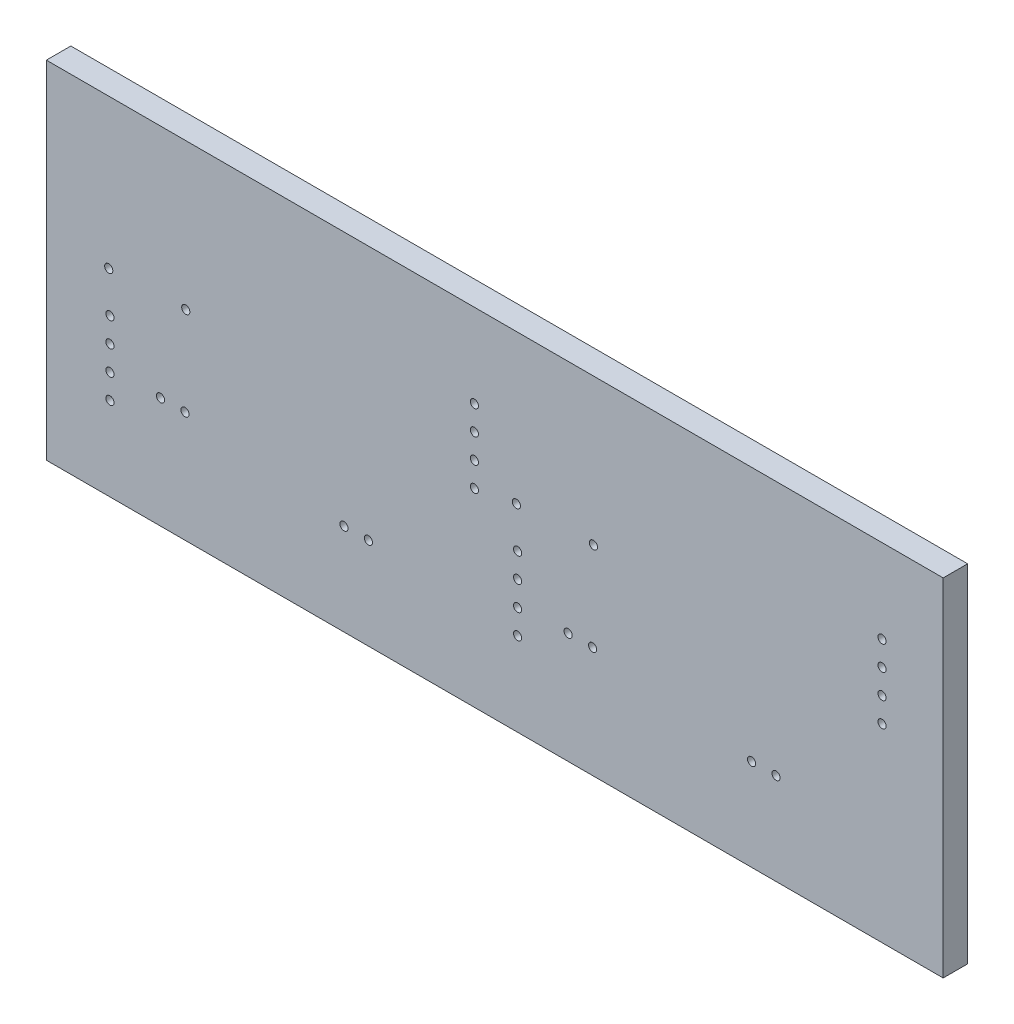
SolidWorks part; units mm, degrees
ref_plane "Plan de face" through (0, 0, 0) normal (0, 0, 1) x (1, 0, 0)
ref_plane "Plan de dessus" through (0, 0, 0) normal (0, 1, 0) x (1, 0, 0)
ref_plane "Plan de droite" through (0, 0, 0) normal (1, 0, 0) x (0, 0, -1)
sketch "Esquisse1" plane through (0, 0, 0) normal (0, 0, 1) x (1, 0, 0)
  line L0 (97.3951, 0) -> (-118.5049, 0) construction
  line L1 (-165, 119) -> (165, 119)
  line L2 (-165, 119) -> (-165, -119)
  line L3 (-165, -119) -> (165, -119)
  line L4 (165, 119) -> (165, -119)
  line L5 (0, 79.3588) -> (0, -79.3588) construction
  line L6 (-92.5, -55) -> (-77.5, -55)
  line L7 (-92.5, -55) -> (-92.5, -61)
  line L8 (-92.5, -61) -> (-77.5, -61)
  line L9 (-77.5, -55) -> (-77.5, -61)
  line L10 (-7.5, -55) -> (7.5, -55)
  line L11 (-7.5, -55) -> (-7.5, -61)
  line L12 (-7.5, -61) -> (7.5, -61)
  line L13 (7.5, -55) -> (7.5, -61)
  line L14 (77.5, -55) -> (92.5, -55)
  line L15 (77.5, -55) -> (77.5, -61)
  line L16 (77.5, -61) -> (92.5, -61)
  line L17 (92.5, -55) -> (92.5, -61)
  line L18 (-225.3679, 76) -> (203.1013, 76) construction
  line L19 (55, 99) -> (75, 99)
  line L20 (55, 99) -> (55, 93)
  line L21 (55, 93) -> (75, 93)
  line L22 (75, 99) -> (75, 93)
  line L23 (85, 99) -> (105, 99)
  line L24 (85, 99) -> (85, 93)
  line L25 (85, 93) -> (105, 93)
  line L26 (105, 99) -> (105, 93)
  circle A0 centre (-125, 76) radius 8
  circle A1 centre (125, 76) radius 8
  dimension "D23" = 16
  dimension "D24" = 16
  dimension "D1" = 238
  dimension "D2" = 330
  dimension "D3" = 165
  dimension "D4" = 119
  dimension "D5" = 15
  dimension "D6" = 6
  dimension "D7" = 6
  dimension "D8" = 15
  dimension "D9" = 6
  dimension "D10" = 15
  dimension "D11" = 70
  dimension "D12" = 70
  dimension "D13" = 58
  dimension "D14" = 72.5
  dimension "D15" = 6
  dimension "D16" = 20
  dimension "D17" = 20
  dimension "D18" = 6
  dimension "D19" = 10
  dimension "D20" = 60
  dimension "D21" = 20
  dimension "D22" = 20
  dimension "D25" = 40
  dimension "D26" = 40
  dimension "D27" = 195
extrude "Boss.-Extru.1" add sketch "Esquisse1" along normal blind 6
sketch "Esquisse2" plane through (0, 0, 6) normal (0, 0, 1) x (1, 0, 0)
  line L0 (243.146, 0) -> (-260.0003, 0) construction
  line L1 (0, 180.4713) -> (0, -129.6072) construction
  line L2 (175, 124) -> (-175, 124) construction
  line L3 (-125, 124) -> (-105, 124)
  line L4 (-125, 124) -> (-125, 130)
  line L5 (-125, 130) -> (-105, 130)
  line L6 (-105, 124) -> (-105, 130)
  line L7 (-175, 124) -> (-175, -124) construction
  line L8 (-55, 124) -> (-35, 124)
  line L9 (-55, 124) -> (-55, 130)
  line L10 (-55, 130) -> (-35, 130)
  line L11 (-35, 124) -> (-35, 130)
  line L12 (35, 124) -> (35, 130)
  line L13 (55, 130) -> (35, 130)
  line L14 (55, 124) -> (55, 130)
  line L15 (55, 124) -> (35, 124)
  line L16 (105, 124) -> (105, 130)
  line L17 (125, 130) -> (105, 130)
  line L18 (125, 124) -> (125, 130)
  line L19 (125, 124) -> (105, 124)
  line L20 (-125, 124) -> (-105, 124)
  line L21 (-125, 124) -> (-125, 130)
  line L22 (-125, 130) -> (-105, 130)
  line L23 (-105, 124) -> (-105, 130)
  line L24 (-55, 124) -> (-35, 124)
  line L25 (-55, 124) -> (-55, 130)
  line L26 (-55, 130) -> (-35, 130)
  line L27 (-35, 124) -> (-35, 130)
  line L28 (35, 124) -> (35, 130)
  line L29 (55, 130) -> (35, 130)
  line L30 (55, 124) -> (55, 130)
  line L31 (55, 124) -> (35, 124)
  line L32 (105, 124) -> (105, 130)
  line L33 (125, 130) -> (105, 130)
  line L34 (125, 124) -> (125, 130)
  line L35 (125, 124) -> (105, 124)
  line L36 (125, -124) -> (105, -124)
  line L37 (125, -124) -> (125, -130)
  line L38 (125, -130) -> (105, -130)
  line L39 (105, -124) -> (105, -130)
  line L40 (55, -124) -> (35, -124)
  line L41 (55, -124) -> (55, -130)
  line L42 (55, -130) -> (35, -130)
  line L43 (35, -124) -> (35, -130)
  line L44 (-35, -124) -> (-35, -130)
  line L45 (-55, -130) -> (-35, -130)
  line L46 (-55, -124) -> (-55, -130)
  line L47 (-55, -124) -> (-35, -124)
  line L48 (-105, -124) -> (-105, -130)
  line L49 (-125, -130) -> (-105, -130)
  line L50 (-125, -124) -> (-125, -130)
  line L51 (-125, -124) -> (-105, -124)
  line L52 (125, -124) -> (105, -124)
  line L53 (125, -124) -> (125, -130)
  line L54 (125, -130) -> (105, -130)
  line L55 (105, -124) -> (105, -130)
  line L56 (55, -124) -> (35, -124)
  line L57 (55, -124) -> (55, -130)
  line L58 (55, -130) -> (35, -130)
  line L59 (35, -124) -> (35, -130)
  line L60 (-35, -124) -> (-35, -130)
  line L61 (-55, -130) -> (-35, -130)
  line L62 (-55, -124) -> (-55, -130)
  line L63 (-55, -124) -> (-35, -124)
  line L64 (-105, -124) -> (-105, -130)
  line L65 (-125, -130) -> (-105, -130)
  line L66 (-125, -124) -> (-125, -130)
  line L67 (-125, -124) -> (-105, -124)
  line M9 (-175, -124) -> (175, -124)
  line M11 (175, 124) -> (-175, 124)
  dimension "D1" = 6
  dimension "D2" = 6
  dimension "D3" = 20
  dimension "D4" = 20
  dimension "D5" = 50
  dimension "D6" = 50
extrude "Boss.-Extru.2" add sketch "Esquisse2" against normal blind 6 contours L6 L5 L4 M11 | L11 L10 L9 M11 | L14 L13 L12 M11 | L18 L17 L16 M11 | L39 L38 L37 M9 | L43 L42 L41 M9 | L46 L45 L44 M9 | L50 L49 L48 M9
sketch "Esquisse3" plane through (0, 0, 6) normal (0, 0, 1) x (1, 0, 0)
  line L0 (-175, 124) -> (-175, -124) construction
  line L1 (-175, 74) -> (-169, 74)
  line L2 (-175, 74) -> (-175, 94)
  line L3 (-175, 94) -> (-169, 94)
  line L4 (-169, 74) -> (-169, 94)
  line L5 (234.1368, 0) -> (-337.9213, 0) construction
  line L6 (-175, 34) -> (-169, 34)
  line L7 (-175, 34) -> (-175, 14)
  line L8 (-175, 14) -> (-169, 14)
  line L9 (-169, 34) -> (-169, 14)
  line L10 (0, 279.7488) -> (0, -188.1201) construction
  line L11 (-125, 124) -> (-175, 124) construction
  line L12 (-169, -34) -> (-169, -14)
  line L13 (-175, -14) -> (-169, -14)
  line L14 (-175, -34) -> (-175, -14)
  line L15 (-175, -34) -> (-169, -34)
  line L16 (-169, -74) -> (-169, -94)
  line L17 (-175, -94) -> (-169, -94)
  line L18 (-175, -74) -> (-175, -94)
  line L19 (-175, -74) -> (-169, -74)
  line L20 (175, -74) -> (169, -74)
  line L21 (175, -74) -> (175, -94)
  line L22 (175, -94) -> (169, -94)
  line L23 (169, -74) -> (169, -94)
  line L24 (175, -34) -> (169, -34)
  line L25 (175, -34) -> (175, -14)
  line L26 (175, -14) -> (169, -14)
  line L27 (169, -34) -> (169, -14)
  line L28 (169, 34) -> (169, 14)
  line L29 (175, 14) -> (169, 14)
  line L30 (175, 34) -> (175, 14)
  line L31 (175, 34) -> (169, 34)
  line L32 (169, 74) -> (169, 94)
  line L33 (175, 94) -> (169, 94)
  line L34 (175, 74) -> (175, 94)
  line L35 (175, 74) -> (169, 74)
  line L36 (163, -124) -> (163, -114)
  line L37 (-175, -124) -> (-163, -124)
  line L38 (-175, -124) -> (-175, -114)
  line L39 (-175, -114) -> (-163, -114)
  line L40 (-163, -124) -> (-163, -114)
  line L41 (175, -114) -> (163, -114)
  line L42 (175, -124) -> (175, -114)
  line L43 (175, -124) -> (163, -124)
  dimension "D1" = 40
  dimension "D2" = 6
  dimension "D3" = 6
  dimension "D4" = 20
  dimension "D5" = 20
  dimension "D6" = 30
  dimension "D7" = 12
  dimension "D8" = 10
extrude "Enlèv. mat.-Extru.1" cut sketch "Esquisse3" against normal blind 6
sketch "Esquisse4" plane through (0, 0, 6) normal (0, 0, 1) x (1, 0, 0)
  line L0 (-172, 127) -> (-172, -131.0602) construction
  line L1 (0, 158.5579) -> (0, -182.4489) construction
  line L2 (-125, 124) -> (-175, 124) construction
  line L3 (-106.4439, -58) -> (117.3944, -58) construction
  line L4 (-169, 94) -> (-175, 94) construction
  line L5 (-175, 124) -> (-175, 94) construction
  line L6 (-175, 74) -> (-169, 74) construction
  line L7 (-169, 34) -> (-175, 34) construction
  line L8 (-175, 14) -> (-169, 14) construction
  line L9 (-169, -14) -> (-175, -14) construction
  line L10 (-102.5, -60) -> (-102.5, -66) construction
  line L11 (-87.5, -66) -> (-87.5, -60) construction
  line L12 (-175, -34) -> (-169, -34) construction
  line L13 (-169, -74) -> (-175, -74) construction
  line L14 (-175, -94) -> (-169, -94) construction
  line L15 (-17.5, -60) -> (-17.5, -66) construction
  line L16 (172, 127) -> (172, -131.0602) construction
  line L17 (136.5184, 101) -> (43.4816, 101) construction
  line L18 (-126.5544, 127) -> (2.7821, 127) construction
  line L19 (-55, 124) -> (-105, 124) construction
  line L20 (-55, 124) -> (-55, 130) construction
  line L21 (85, 98) -> (85, 104) construction
  line L23 (65, 98) -> (85, 98) construction
  circle A0 centre (-172, 119) radius 1.5
  circle A1 centre (-172, 99) radius 1.5
  circle A2 centre (-172, 69) radius 1.5
  circle A3 centre (-172, 39) radius 1.5
  circle A4 centre (-172, 9) radius 1.5
  circle A5 centre (-115, 127) radius 1.5
  circle A6 centre (-172, -9) radius 1.5
  circle A7 centre (-172, -39) radius 1.5
  circle A8 centre (-172, -69) radius 1.5
  circle A9 centre (-172, -99) radius 1.5
  circle A10 centre (-107.5, -58) radius 1.5
  circle A11 centre (-82.5, -58) radius 1.5
  circle A12 centre (172, -99) radius 1.5
  circle A13 centre (172, -69) radius 1.5
  circle A14 centre (172, -39) radius 1.5
  circle A15 centre (172, -9) radius 1.5
  circle A16 centre (90, 101) radius 1.5
  circle A17 centre (172, 9) radius 1.5
  circle A18 centre (172, 39) radius 1.5
  circle A19 centre (172, 69) radius 1.5
  circle A20 centre (172, 99) radius 1.5
  circle A21 centre (172, 119) radius 1.5
  circle A22 centre (-22.5, -58) radius 1.5
  circle A23 centre (22.5, -58) radius 1.5
  circle A24 centre (82.5, -58) radius 1.5
  circle A25 centre (107.5, -58) radius 1.5
  circle A26 centre (-45, 127) radius 1.5
  circle A27 centre (45, 127) radius 1.5
  circle A28 centre (115, 127) radius 1.5
  dimension "D1" = 3
  dimension "D2" = 3
  dimension "D3" = 3
  dimension "D4" = 3
  dimension "D5" = 3
  dimension "D6" = 3
  dimension "D7" = 3
  dimension "D8" = 3
  dimension "D9" = 3
  dimension "D10" = 3
  dimension "D11" = 3
  dimension "D12" = 5
  dimension "D13" = 5
  dimension "D15" = 5
  dimension "D16" = 5
  dimension "D17" = 5
  dimension "D19" = 3
  dimension "D20" = 5
  dimension "D21" = 5
  dimension "D23" = 3
  dimension "D24" = 3
  dimension "D25" = 5
  dimension "D26" = 5
  dimension "D27" = 5
  dimension "D28" = 10
  dimension "D29" = 3
  dimension "D30" = 5
  dimension "D31" = 3
  dimension "D33" = 10
  dimension "D14" = 3
  dimension "D18" = 5
  dimension "D22" = 5
  dimension "D32" = 3
extrude "Enlèv. mat.-Extru.2" cut sketch "Esquisse4" against normal blind 6
sketch "Esquisse5" plane through (0, 0, 6) normal (0, 0, 1) x (1, 0, 0)
  line L1 (-200.0968, 0) -> (223.5072, 0)
  line L2 (-200.0968, 0) -> (-200.0968, -150.3561)
  line L3 (-200.0968, -150.3561) -> (223.5072, -150.3561)
  line L4 (223.5072, 0) -> (223.5072, -150.3561)
extrude "Enlèv. mat.-Extru.3" cut sketch "Esquisse5" against normal blind 6
sketch "Esquisse6" plane through (0, 0, 6) normal (0, 0, 1) x (1, 0, 0)
  line L0 (-175, 74) -> (-175, 34) construction
  line L2 (175, 0) -> (-175, 0) construction
  text T0 "SUDRIABOTIK" font "Century Gothic" height in points 72
  dimension "D1" = 93.8
  dimension "D2" = 29.5
extrude "Enlèv. mat.-Extru.4" cut sketch "Esquisse6" against normal blind 6
sketch "Esquisse8" plane through (0, 0, 6) normal (0, 0, 1) x (1, 0, 0)
  line L0 (-105, 85) -> (-105, 0)
  line L1 (175, 0) -> (-175, 0) construction
  line L2 (-105, 0) -> (-187.5965, 0)
  line L3 (-187.5965, 0) -> (-187.5965, 141.8457)
  line L4 (-187.5965, 141.8457) -> (211.3777, 141.8457)
  line L5 (211.3777, 141.8457) -> (211.3777, 0)
  line L6 (211.3777, 0) -> (115, 0)
  line L7 (115, 0) -> (115, 85)
  line L8 (115, 85) -> (-105, 85)
  line L9 (175, 0) -> (175, 14) construction
  dimension "D1" = 220
  dimension "D2" = 85
  dimension "D3" = 60
  dimension "D5" = 24.2885
extrude "Enlèv. mat.-Extru.5" cut sketch "Esquisse8" against normal blind 6
sketch "Esquisse10" plane through (0, 0, 0) normal (0, 0, -1) x (-1, 0, 0)
  line L0 (-110, 0) -> (-110, 80)
  line L1 (-115, 0) -> (105, 0) construction
  line L2 (-110, 80) -> (100, 80)
  line L3 (100, 80) -> (100, 0)
  line L4 (105, 85) -> (-115, 85) construction
  line L5 (105, 0) -> (105, 85) construction
  line L6 (-115, 85) -> (-115, 0) construction
  dimension "D1" = 5
  dimension "D2" = 5
  dimension "D3" = 5
sketch "Esquisse11" plane through (0, 0, 6) normal (0, 0, 1) x (1, 0, 0)
  line L0 (-105, 0) -> (-105, 85) construction
  line L1 (-90, 67.8756) -> (100, 67.8756)
  line L2 (-90, 67.8756) -> (-90, 17.8756)
  line L3 (-90, 17.8756) -> (100, 17.8756)
  line L4 (100, 67.8756) -> (100, 17.8756)
  line L5 (115, 85) -> (115, 0) construction
  dimension "D1" = 50
  dimension "D3" = 15
  dimension "D4" = 15
extrude "Boss.-Extru.3" add sketch "Esquisse11" against normal blind 6
sketch "Esquisse12" plane through (0, 0, 6) normal (0, 0, 1) x (1, 0, 0)
  line L0 (-105, 0) -> (-105, 85) construction
  line L1 (-95, 67.5) -> (5, 67.5)
  line L2 (-95, 67.5) -> (-95, 17.5)
  line L3 (-95, 17.5) -> (5, 17.5)
  line L4 (5, 67.5) -> (5, 17.5)
  line L5 (5, 67.5) -> (105, 67.5)
  line L6 (5, 67.5) -> (5, 17.5)
  line L7 (5, 17.5) -> (105, 17.5)
  line L8 (105, 67.5) -> (105, 17.5)
  line L9 (-105, 85) -> (115, 85) construction
  circle A0 centre (0, 64.5) radius 1
  circle A1 centre (0, 58.5) radius 1
  circle A2 centre (0, 52.5) radius 1
  circle A3 centre (0, 46.5) radius 1
  circle A4 centre (-26, 22.5) radius 1
  circle A5 centre (-32, 22.5) radius 1
  circle A6 centre (-77, 27.2361) radius 1
  circle A7 centre (-71, 27.2361) radius 1
  circle A8 centre (-89.4, 38.5) radius 1
  circle A9 centre (-89.4, 32.5) radius 1
  circle A10 centre (-89.4, 26.5) radius 1
  circle A11 centre (-89.4, 20.5) radius 1
  circle A12 centre (-89.7, 48.4) radius 1
  circle A13 centre (-70.8, 49.1) radius 1
  circle A14 centre (100, 64.5) radius 1
  circle A15 centre (100, 58.5) radius 1
  circle A16 centre (100, 52.5) radius 1
  circle A17 centre (100, 46.5) radius 1
  circle A18 centre (74, 22.5) radius 1
  circle A19 centre (68, 22.5) radius 1
  circle A20 centre (23, 27.2361) radius 1
  circle A21 centre (29, 27.2361) radius 1
  circle A22 centre (10.6, 38.5) radius 1
  circle A23 centre (10.6, 32.5) radius 1
  circle A24 centre (10.6, 26.5) radius 1
  circle A25 centre (10.6, 20.5) radius 1
  circle A26 centre (10.3, 48.4) radius 1
  circle A27 centre (29.2, 49.1) radius 1
  dimension "D3" = 3
  dimension "D5" = 2
  dimension "D6" = 6
  dimension "D7" = 6
  dimension "D8" = 5
  dimension "D9" = 5
  dimension "D10" = 2
  dimension "D11" = 2
  dimension "D12" = 5
  dimension "D13" = 6
  dimension "D14" = 31
  dimension "D16" = 5
  dimension "D17" = 6
  dimension "D18" = 18
  dimension "D19" = 6
  dimension "D20" = 3
  dimension "D25" = 5.3
  dimension "D27" = 18.4
  dimension "D28" = 24.2
  dimension "D1" = 50
  dimension "D2" = 100
  dimension "D4" = 5
  dimension "D15" = 5
  dimension "D21" = 6
  dimension "D22" = 6
  dimension "D23" = 6
  dimension "D24" = 5.6
  dimension "D26" = 19.1
  dimension "D29" = 10
  dimension "D31" = 17.5
  dimension "D30" = 2
extrude "Enlèv. mat.-Extru.8" cut sketch "Esquisse12" against normal blind 6 contours A14 | A15 | A16 | A17 | A18 | A19 | A21 | A20 | A25 | A24 | A23 | A22 | A26 | A27 | A0 | A1 | A2 | A3 | A4 | A5 | A7 | A6 | A11 | A10 | A9 | A8 | A12 | A13
equation "\"D3@Esquisse1\"=\"D2@Esquisse1\"/2"
equation "\"D4@Esquisse1\"=\"D1@Esquisse1\"/2"
